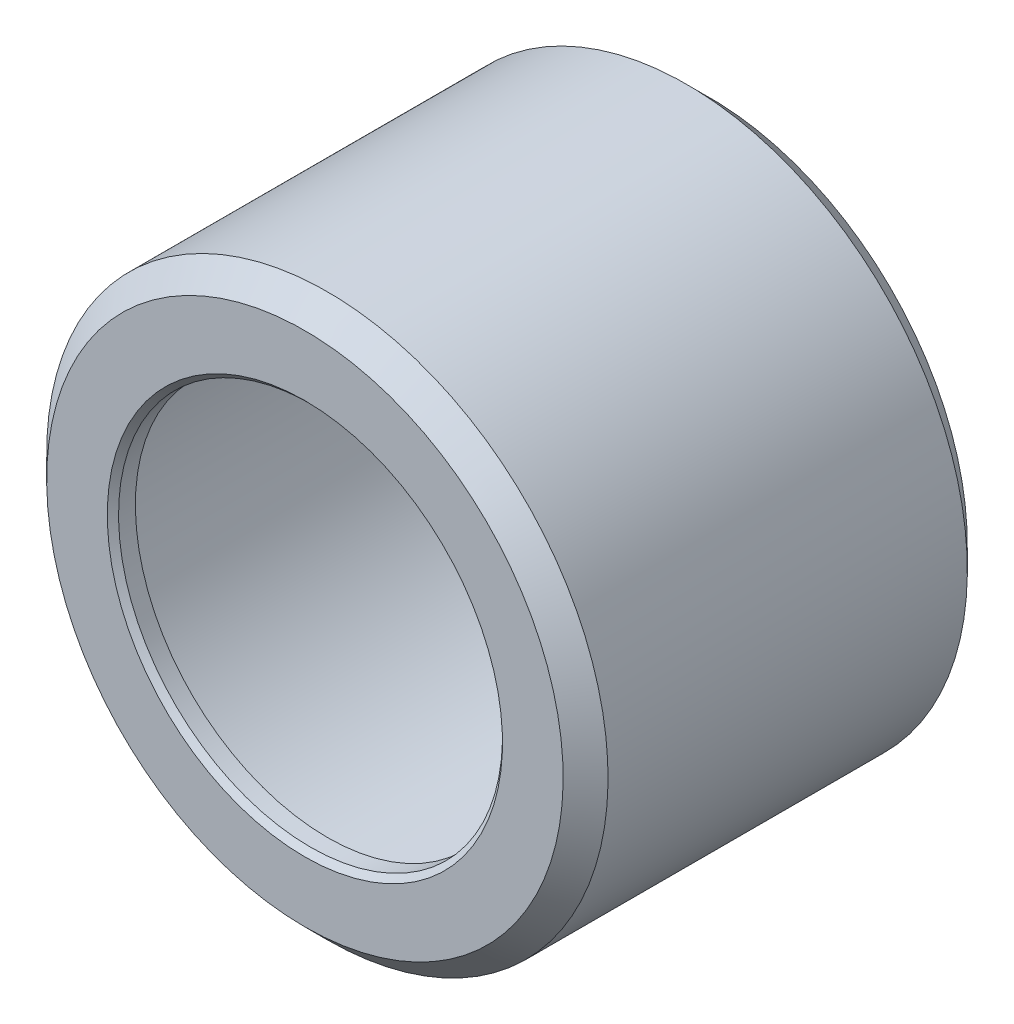
SolidWorks part; units mm, degrees
ref_plane "Piano frontale" through (0, 0, 0) normal (0, 0, 1) x (1, 0, 0)
ref_plane "Piano superiore" through (0, 0, 0) normal (0, 1, 0) x (1, 0, 0)
ref_plane "Piano destro" through (0, 0, 0) normal (1, 0, 0) x (0, 0, -1)
sketch "Schizzo5" plane through (0, 0, 0) normal (1, 0, 0) x (0, 0, -1)
  line L0 (0, 0) -> (-9, 0) construction
  line L1 (-9, 0) -> (-9, 8.55) construction
  line L2 (-9, 8.55) -> (-9, 11.5)
  line L3 (-8, 12.5) -> (8, 12.5)
  line L4 (9, 11.5) -> (9, 8.55)
  line L5 (-9, 11.5) -> (-8, 12.5)
  line L6 (8, 12.5) -> (9, 11.5)
  point P2 (-9, 12.5)
  point P5 (9, 12.5)
  dimension "D1" = 9
  dimension "D2" = 12.5
  dimension "D3" = 3.95
  dimension "D4" = 18
surface "Superficie-Rivoluzione1" sketch "Schizzo5" parameters "D1"=360
thicken "Spessore1" thickness 1 parameters "D1"=1
chamfer "Smusso1" distance 0.25 angle 45 2 edges at (0, -8.55, -9) (0, -8.55, 9)
